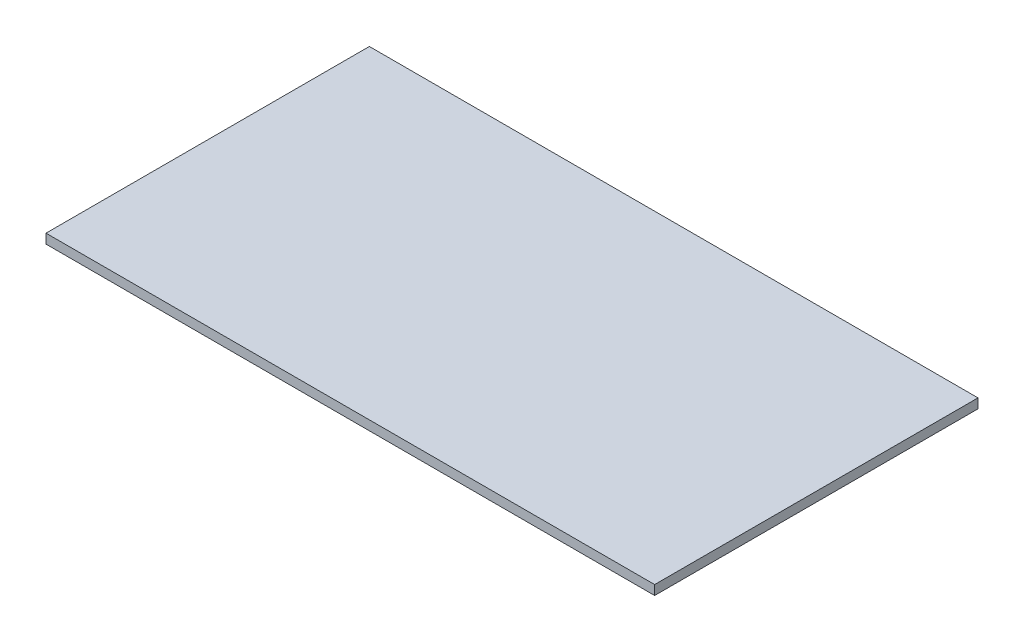
SolidWorks part; units mm, degrees
material "Balsa"
ref_plane "Front Plane" through (0, 0, 0) normal (0, 0, 1) x (1, 0, 0)
ref_plane "Top Plane" through (0, 0, 0) normal (0, 1, 0) x (1, 0, 0)
ref_plane "Right Plane" through (0, 0, 0) normal (1, 0, 0) x (0, 0, -1)
sketch "Sketch1" plane through (0, 0, 0) normal (0, 1, 0) x (1, 0, 0)
  line L1 (-480, -255) -> (480, -255)
  line L2 (-480, -255) -> (-480, 255)
  line L3 (-480, 255) -> (480, 255)
  line L4 (480, -255) -> (480, 255)
  line L5 (-480, -255) -> (480, 255) construction
  line L6 (-480, 255) -> (480, -255) construction
  point P0 (0, 0)
  dimension "D1" = 510
  dimension "D2" = 960
extrude "Boss-Extrude1" add sketch "Sketch1" along normal mid plane 15
